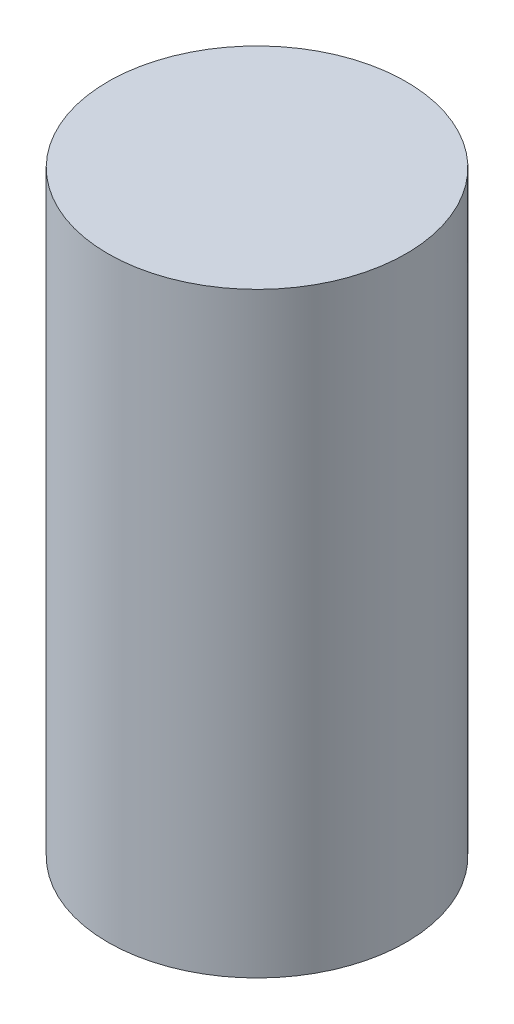
SolidWorks part; units mm, degrees
ref_plane "Front Plane" through (0, 0, 0) normal (0, 0, 1) x (1, 0, 0)
ref_plane "Top Plane" through (0, 0, 0) normal (0, 1, 0) x (1, 0, 0)
ref_plane "Right Plane" through (0, 0, 0) normal (1, 0, 0) x (0, 0, -1)
sketch "Sketch1" plane through (0, 0, 0) normal (0, 1, 0) x (1, 0, 0)
  circle A0 centre (0, 0) radius 5
  dimension "D1" = 10
extrude "Boss-Extrude1" add sketch "Sketch1" along normal blind 20
